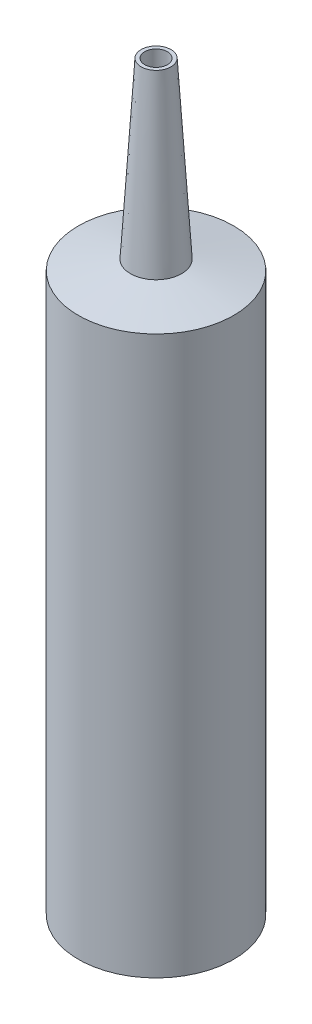
SolidWorks part; units mm, degrees
ref_plane "前视基准面" through (0, 0, 0) normal (0, 0, 1) x (1, 0, 0)
ref_plane "上视基准面" through (0, 0, 0) normal (0, 1, 0) x (1, 0, 0)
ref_plane "右视基准面" through (0, 0, 0) normal (1, 0, 0) x (0, 0, -1)
sketch "草图1" plane through (0, 0, 0) normal (0, 0, 1) x (1, 0, 0)
  line L0 (14.5, 111) -> (14.5, 0)
  line L1 (14.5, 0) -> (15.6, 0)
  line L2 (15.6, 0) -> (15.6, 112.0368)
  line L3 (15.6, 112.0368) -> (5.1364, 114.0707)
  line L4 (5.1364, 114.0707) -> (3, 149)
  line L5 (3, 149) -> (2.276, 149)
  line L6 (2.276, 149) -> (4.8, 111)
  line L7 (4.8, 111) -> (14.5, 111)
  line L8 (0, 149) -> (0, 0) construction
revolve "旋转1" add sketch "草图1" angle 360 about L8
